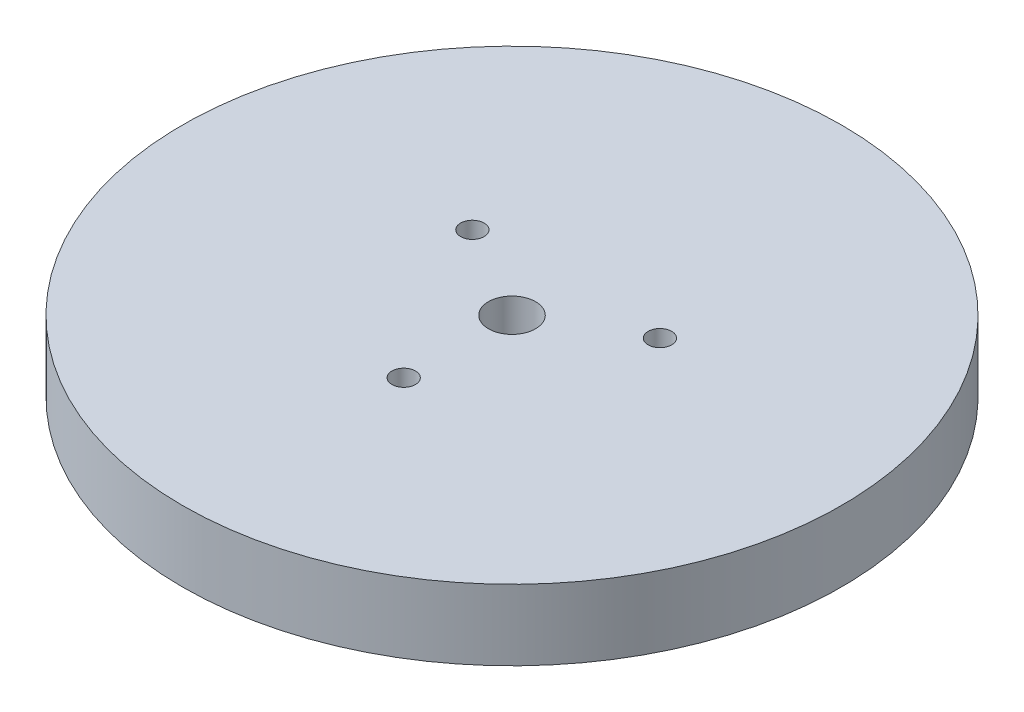
SolidWorks part; units mm, degrees
ref_plane "Front Plane" through (0, 0, 0) normal (0, 0, 1) x (1, 0, 0)
ref_plane "Top Plane" through (0, 0, 0) normal (0, 1, 0) x (1, 0, 0)
ref_plane "Right Plane" through (0, 0, 0) normal (1, 0, 0) x (0, 0, -1)
sketch "Sketch1" plane through (0, 0, 0) normal (0, 1, 0) x (1, 0, 0)
  circle A0 centre (0, 0) radius 70
  dimension "D1" = 140
extrude "Boss-Extrude1" add sketch "Sketch1" along normal blind 15
sketch "Sketch2" plane through (0, 15, 0) normal (0, 1, 0) x (1, 0, 0)
  circle A0 centre (0, 0) radius 5
  circle A1 centre (0, 0) radius 70 construction
  dimension "D1" = 10
extrude "Cut-Extrude1" cut sketch "Sketch2" against normal blind 15
sketch "Sketch3" plane through (0, 0, 0) normal (0, -1, 0) x (1, 0, 0)
  line L0 (0, 23) -> (0, 0) construction
  line L1 (0, 0) -> (-19.9186, -11.5) construction
  line L3 (0, 0) -> (19.9186, -11.5) construction
  circle A0 centre (0, 23) radius 2.5
  circle A1 centre (19.9186, -11.5) radius 2.5
  circle A2 centre (-19.9186, -11.5) radius 2.5
  dimension "D1" = 23
  dimension "D3" = 120
  dimension "D2" = 5
  dimension "D4" = 23
  dimension "D5" = 120
  dimension "D6" = 120
extrude "Cut-Extrude2" cut sketch "Sketch3" against normal through all
